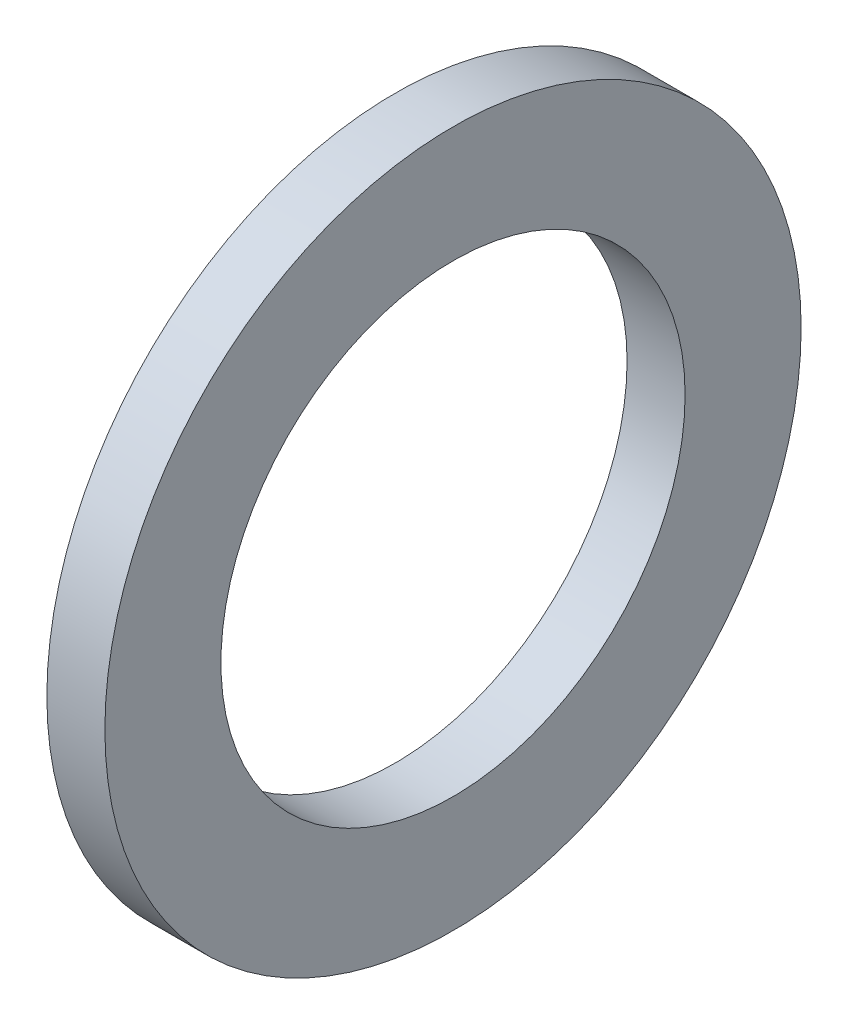
SolidWorks part; units mm, degrees
material "Brass"
ref_plane "Front Plane" through (0, 0, 0) normal (0, 0, 1) x (1, 0, 0)
ref_plane "Top Plane" through (0, 0, 0) normal (0, 1, 0) x (1, 0, 0)
ref_plane "Right Plane" through (0, 0, 0) normal (1, 0, 0) x (0, 0, -1)
sketch "Sketch1" plane through (0, 0, 0) normal (1, 0, 0) x (0, 0, -1)
  circle A0 centre (0, 0) radius 12.7
  circle A1 centre (0, 0) radius 19.05
  dimension "D1" = 38.1
  dimension "D2" = 25.4
extrude "Boss-Extrude1" add sketch "Sketch1" along normal blind 3.175
